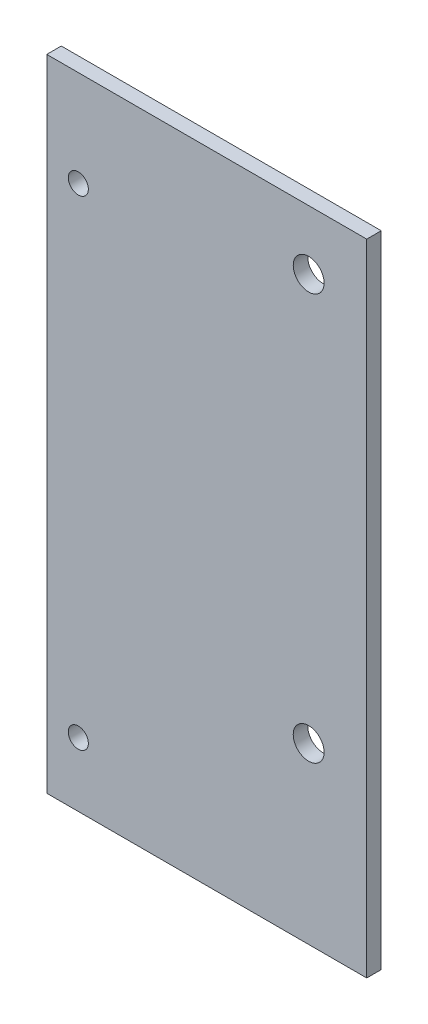
SolidWorks part; units mm, degrees
ref_plane "Front Plane" through (0, 0, 0) normal (0, 0, 1) x (1, 0, 0)
ref_plane "Top Plane" through (0, 0, 0) normal (0, 1, 0) x (1, 0, 0)
ref_plane "Right Plane" through (0, 0, 0) normal (1, 0, 0) x (0, 0, -1)
sketch "Sketch1" plane through (0, 0, 0) normal (0, 0, 1) x (1, 0, 0)
  line L1 (0, 0) -> (70, 0)
  line L2 (0, 0) -> (0, 140)
  line L3 (0, 140) -> (70, 140)
  line L4 (70, 0) -> (70, 140)
  dimension "D1" = 70
  dimension "D2" = 140
extrude "Boss-Extrude1" add sketch "Sketch1" along normal blind 3.175
sketch "Sketch2" plane through (0, 0, 0) normal (0, 0, -1) x (-1, 0, 0)
  circle A0 centre (-6.9, 119) radius 2.2
  circle A1 centre (-57.3, 127) radius 3.3782
  circle A2 centre (-57.3, 38.1) radius 3.3782
  circle A3 centre (-6.9, 14) radius 2.2
  dimension "D1" = 4.4
  dimension "D2" = 6.7564
  dimension "D3" = 4.4
  dimension "D4" = 6.7564
extrude "Cut-Extrude1" cut sketch "Sketch2" against normal through all
